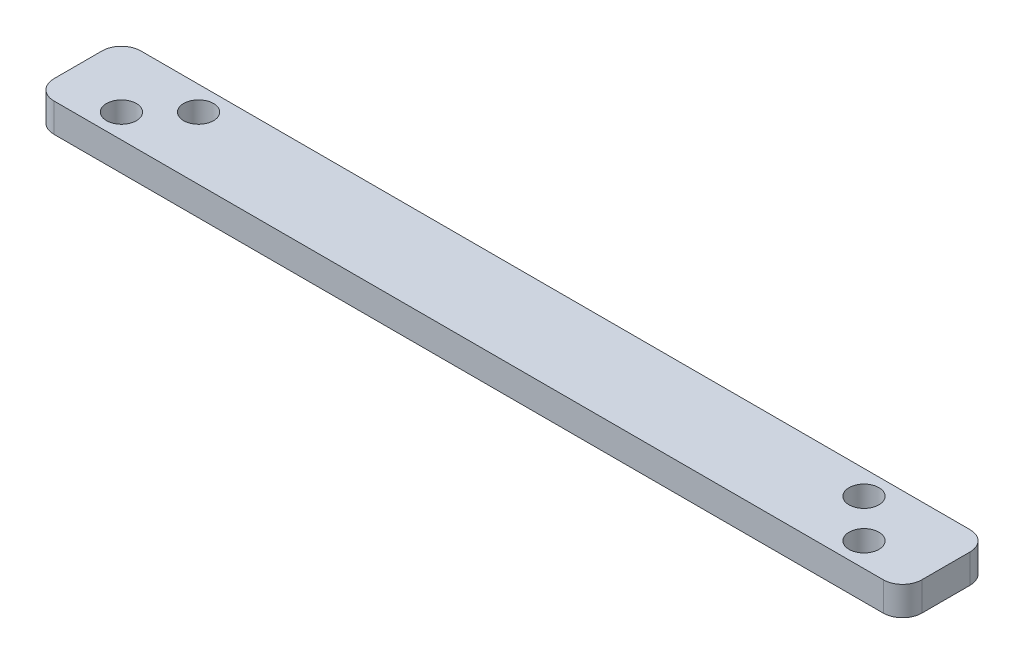
SolidWorks part; units mm, degrees
ref_plane "前视基准面" through (0, 0, 0) normal (0, 0, 1) x (1, 0, 0)
ref_plane "上视基准面" through (0, 0, 0) normal (0, 1, 0) x (1, 0, 0)
ref_plane "右视基准面" through (0, 0, 0) normal (1, 0, 0) x (0, 0, -1)
sketch "草图1" plane through (0, 0, 0) normal (0, 1, 0) x (1, 0, 0)
  line L0 (0, 0) -> (0, -17.9272) construction
  line L1 (-45, -4.5) -> (45, -4.5)
  line L2 (-45, -4.5) -> (-45, 4.5)
  line L3 (-45, 4.5) -> (45, 4.5)
  line L4 (45, -4.5) -> (45, 4.5)
  line L5 (-45, -4.5) -> (45, 4.5) construction
  line L6 (-45, 4.5) -> (45, -4.5) construction
  line L7 (0, 0) -> (-49.1215, 0) construction
  circle A0 centre (-38.5, -2) radius 1.55
  circle A4 centre (-34.5, 2) radius 1.55
  circle A5 centre (38.5, -2) radius 1.55
  circle A6 centre (34.5, 2) radius 1.55
  point P0 (0, 0)
  dimension "D3" = 3.1
  dimension "D6" = 3.1
  dimension "D1" = 90
  dimension "D2" = 9
  dimension "D4" = 2
  dimension "D5" = 38.5
  dimension "D7" = 2
  dimension "D8" = 4
extrude "凸台-拉伸2" add sketch "草图1" along normal blind 3
fillet "圆角1" radius 2 4 edges at (45, 1.5, -4.5) (45, 1.5, 4.5) (-45, 1.5, -4.5) (-45, 1.5, 4.5)
